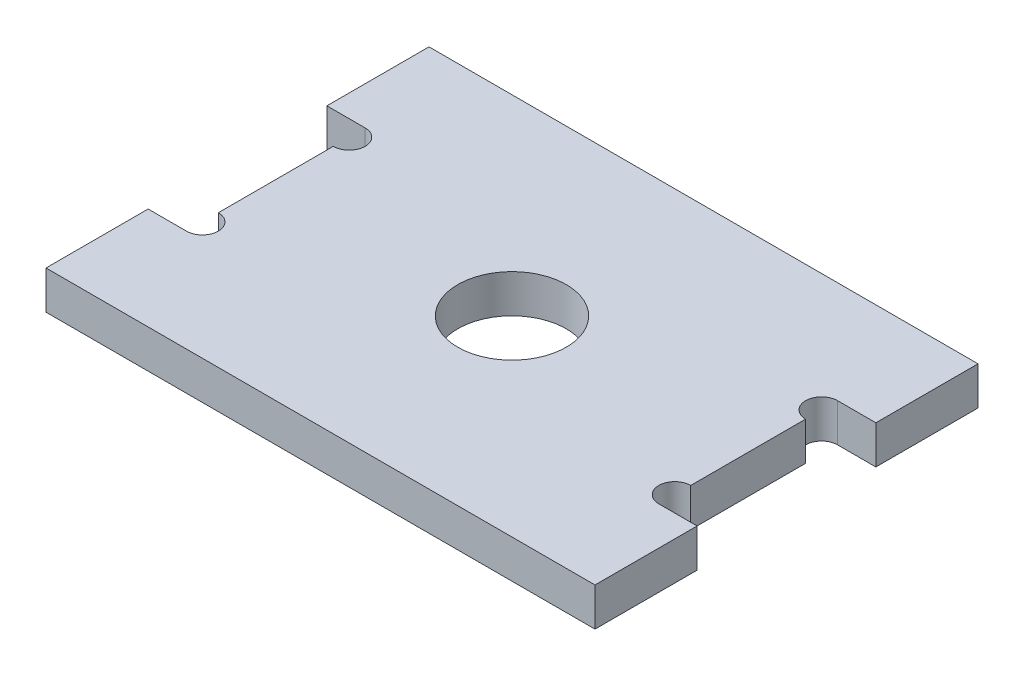
SolidWorks part; units mm, degrees
material "Thornel Mat VMA"
ref_plane "前视基准面" through (0, 0, 0) normal (0, 0, 1) x (1, 0, 0)
ref_plane "上视基准面" through (0, 0, 0) normal (0, 1, 0) x (1, 0, 0)
ref_plane "右视基准面" through (0, 0, 0) normal (1, 0, 0) x (0, 0, -1)
sketch "草图1" plane through (0, 0, 0) normal (0, 1, 0) x (1, 0, 0)
  line L1 (-21.5, 15) -> (21.5, 15)
  line L2 (-21.5, 15) -> (-21.5, -15)
  line L3 (-21.5, -15) -> (21.5, -15)
  line L4 (21.5, 15) -> (21.5, -15)
  line L5 (-21.5, 15) -> (21.5, -15) construction
  line L6 (-21.5, -15) -> (21.5, 15) construction
  circle A0 centre (0, 0) radius 4.25
  dimension "D1" = 8.5
  dimension "D2" = 43
  dimension "D3" = 30
extrude "凸台-拉伸1" add sketch "草图1" along normal blind 3
sketch "草图2" plane through (0, 3, 0) normal (0, 1, 0) x (1, 0, 0)
  line L0 (21.5, -15) -> (21.5, 15) construction
  line L1 (24.5, -7) -> (18.5, -7)
  line L2 (24.5, -7) -> (24.5, 7)
  line L3 (24.5, 7) -> (18.5, 7)
  line L4 (18.5, -7) -> (18.5, 7)
  line L5 (24.5, -7) -> (18.5, 7) construction
  line L6 (24.5, 7) -> (18.5, -7) construction
  line L7 (-21.5, -15) -> (21.5, -15) construction
  line L8 (0, 0) -> (0, -14.7042) construction
  line L9 (-24.5, 7) -> (-18.5, 7)
  line L10 (-18.5, -7) -> (-18.5, 7)
  line L11 (-24.5, -7) -> (-24.5, 7)
  line L12 (-24.5, -7) -> (-18.5, -7)
  line L13 (-21.5, 15) -> (-21.5, -15) construction
  point P0 (21.5, 0)
  dimension "D1" = 3
  dimension "D2" = 8
extrude "切除-拉伸1" cut sketch "草图2" against normal up to surface (3 mm away) up to face at (0, 0, 0)
sketch "草图3" plane through (0, 0, 0) normal (0, -1, 0) x (1, 0, 0)
  line L0 (-18.5, -7) -> (-18.5, 7) construction
  line L1 (0, 0) -> (0, 10.6219) construction
  circle A0 centre (-18.5, 5.75) radius 1.25
  circle A1 centre (-18.5, -5.75) radius 1.25
  circle A2 centre (18.5, -5.75) radius 1.25
  circle A3 centre (18.5, 5.75) radius 1.25
  dimension "D1" = 2.5
  dimension "D2" = 2.5
extrude "切除-拉伸2" cut sketch "草图3" against normal up to next
sketch "草图4" plane through (0, 3, 0) normal (0, 1, 0) x (1, 0, 0)
  line L0 (0, 0) -> (18.5, 0) construction
  line L1 (18.5, 4.5) -> (18.5, -4.5) construction
  line L2 (0, 0) -> (0, -15) construction
  line L3 (-21.5, -15) -> (21.5, -15) construction
